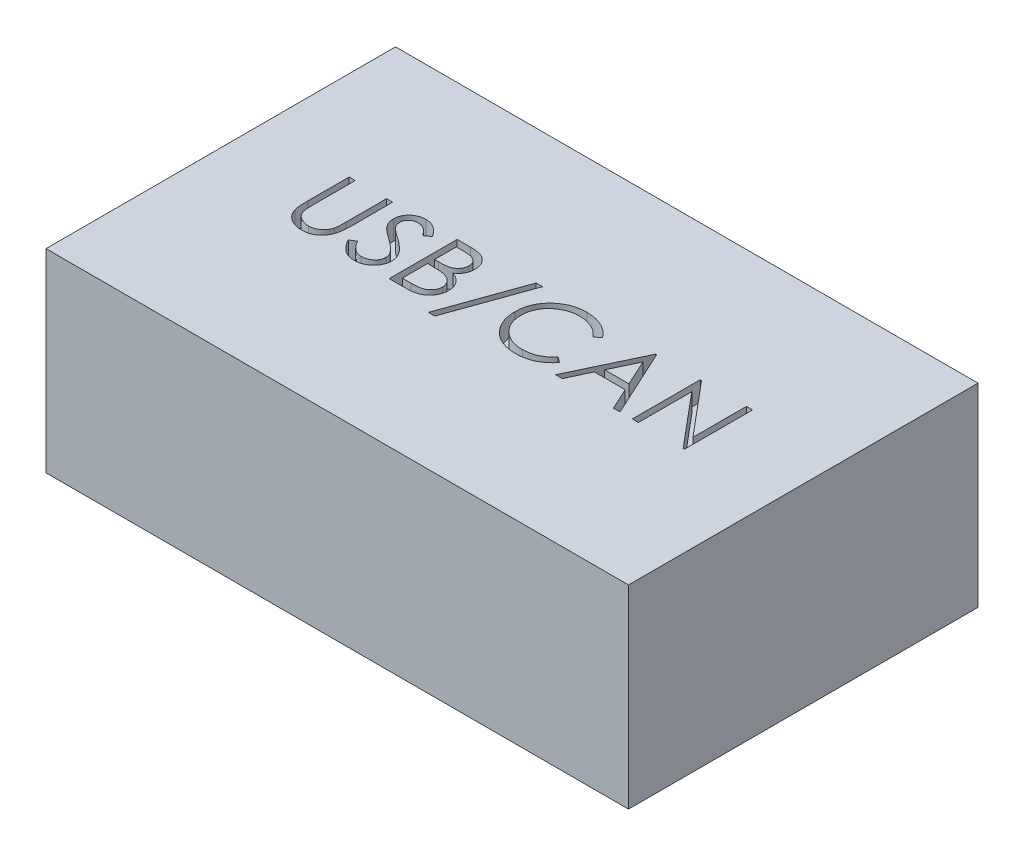
SolidWorks part; units mm, degrees
ref_plane "Front Plane" through (0, 0, 0) normal (0, 0, 1) x (1, 0, 0)
ref_plane "Top Plane" through (0, 0, 0) normal (0, 1, 0) x (1, 0, 0)
ref_plane "Right Plane" through (0, 0, 0) normal (1, 0, 0) x (0, 0, -1)
sketch "Sketch1" plane through (0, 0, 0) normal (0, 1, 0) x (1, 0, 0)
  line L1 (0, 0) -> (30, 0)
  line L2 (0, 0) -> (0, 18)
  line L3 (0, 18) -> (30, 18)
  line L4 (30, 0) -> (30, 18)
  dimension "D1" = 18
  dimension "D2" = 30
extrude "Boss-Extrude1" add sketch "Sketch1" along normal blind 10
sketch "Sketch2" plane through (0, 10, 0) normal (0, 1, 0) x (1, 0, 0)
  line L0 (0, 7.5) -> (30, 7.5) construction
  line L1 (0, 18) -> (0, 0) construction
  line L2 (30, 0) -> (30, 18) construction
  line L3 (0, 0) -> (30, 0) construction
  text T0 "USB/CAN"
  dimension "D1" = 7.5
extrude "Cut-Extrude1" cut sketch "Sketch2" against normal blind 1
